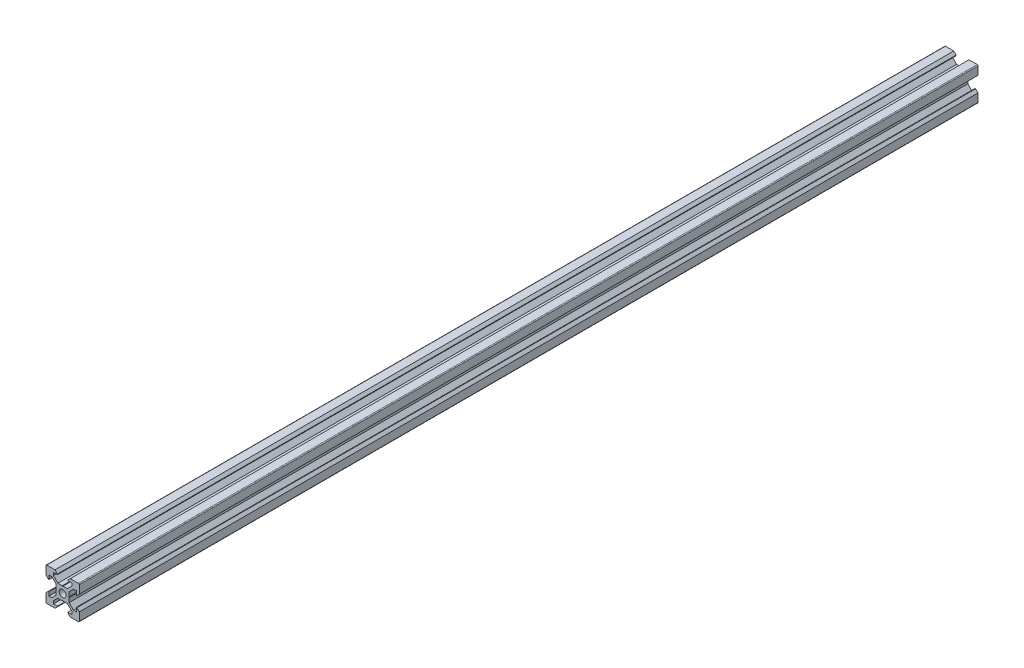
SolidWorks part; units mm, degrees
material "6061-T6 (SS)"
ref_plane "Front Plane" through (0, 0, 0) normal (0, 0, 1) x (1, 0, 0)
ref_plane "Top Plane" through (0, 0, 0) normal (0, 1, 0) x (1, 0, 0)
ref_plane "Right Plane" through (0, 0, 0) normal (1, 0, 0) x (0, 0, -1)
sketch "Sketch1" plane through (0, 0, 0) normal (0, 0, 1) x (1, 0, 0)
  line L1 (9.5, -10) -> (-9.5, -10)
  line L2 (10, -9.5) -> (10, 9.5)
  line L3 (9.5, 10) -> (-9.5, 10)
  line L4 (-10, -9.5) -> (-10, 9.5)
  line L5 (10, -10) -> (-10, 10) construction
  line L6 (10, 10) -> (-10, -10) construction
  circle A0 centre (0, 0) radius 2.1
  arc A1 (-9.5, 10) -> (-10, 9.5) centre (-9.5, 9.5) ccw
  arc A2 (10, 9.5) -> (9.5, 10) centre (9.5, 9.5) ccw
  arc A3 (9.5, -10) -> (10, -9.5) centre (9.5, -9.5) ccw
  arc A4 (-9.5, -10) -> (-10, -9.5) centre (-9.5, -9.5) cw
  point P0 (0, 0)
  line B0 (0, 0) -> (0, 10) construction
  line B1 (0, 3.69) -> (-0.21, 3.9)
  line B2 (-0.21, 3.9) -> (-2.8393, 3.9)
  line B3 (-2.8393, 3.9) -> (-5.5, 6.5607)
  line B4 (-5.5, 6.5607) -> (-5.5, 8.2)
  line B5 (-5.5, 8.2) -> (-3.125, 8.2)
  line B6 (-3.125, 8.2) -> (-3.125, 8.545)
  line B7 (-3.125, 8.545) -> (-4.58, 10)
  line B8 (-4.58, 10) -> (4.58, 10)
  line B9 (0, 0) -> (-5.9132, 5.9132) construction
  line B10 (3.125, 8.545) -> (4.58, 10)
  line B11 (3.125, 8.2) -> (3.125, 8.545)
  line B12 (5.5, 8.2) -> (3.125, 8.2)
  line B13 (5.5, 6.5607) -> (5.5, 8.2)
  line B14 (2.8393, 3.9) -> (5.5, 6.5607)
  line B15 (0.21, 3.9) -> (2.8393, 3.9)
  line B16 (0, 3.69) -> (0.21, 3.9)
  line B17 (0, 0) -> (-10, 0) construction
  line B18 (-3.69, 0) -> (-3.9, -0.21)
  line B19 (-3.9, -0.21) -> (-3.9, -2.8393)
  line B20 (-3.9, -2.8393) -> (-6.5607, -5.5)
  line B21 (-6.5607, -5.5) -> (-8.2, -5.5)
  line B22 (-8.2, -5.5) -> (-8.2, -3.125)
  line B23 (-8.2, -3.125) -> (-8.545, -3.125)
  line B24 (-8.545, -3.125) -> (-10, -4.58)
  line B25 (-10, -4.58) -> (-10, 4.58)
  line B26 (0, 0) -> (-5.9132, -5.9132) construction
  line B27 (-8.545, 3.125) -> (-10, 4.58)
  line B28 (-8.2, 3.125) -> (-8.545, 3.125)
  line B29 (-8.2, 5.5) -> (-8.2, 3.125)
  line B30 (-6.5607, 5.5) -> (-8.2, 5.5)
  line B31 (-3.9, 2.8393) -> (-6.5607, 5.5)
  line B32 (-3.9, 0.21) -> (-3.9, 2.8393)
  line B33 (-3.69, 0) -> (-3.9, 0.21)
  line B34 (0, 0) -> (0, -10) construction
  line B35 (0, -3.69) -> (0.21, -3.9)
  line B36 (0.21, -3.9) -> (2.8393, -3.9)
  line B37 (2.8393, -3.9) -> (5.5, -6.5607)
  line B38 (5.5, -6.5607) -> (5.5, -8.2)
  line B39 (5.5, -8.2) -> (3.125, -8.2)
  line B40 (3.125, -8.2) -> (3.125, -8.545)
  line B41 (3.125, -8.545) -> (4.58, -10)
  line B42 (4.58, -10) -> (-4.58, -10)
  line B43 (0, 0) -> (5.9132, -5.9132) construction
  line B44 (-3.125, -8.545) -> (-4.58, -10)
  line B45 (-3.125, -8.2) -> (-3.125, -8.545)
  line B46 (-5.5, -8.2) -> (-3.125, -8.2)
  line B47 (-5.5, -6.5607) -> (-5.5, -8.2)
  line B48 (-2.8393, -3.9) -> (-5.5, -6.5607)
  line B49 (-0.21, -3.9) -> (-2.8393, -3.9)
  line B50 (0, -3.69) -> (-0.21, -3.9)
  line B51 (0, 0) -> (10, 0) construction
  line B52 (3.69, 0) -> (3.9, 0.21)
  line B53 (3.9, 0.21) -> (3.9, 2.8393)
  line B54 (3.9, 2.8393) -> (6.5607, 5.5)
  line B55 (6.5607, 5.5) -> (8.2, 5.5)
  line B56 (8.2, 5.5) -> (8.2, 3.125)
  line B57 (8.2, 3.125) -> (8.545, 3.125)
  line B58 (8.545, 3.125) -> (10, 4.58)
  line B59 (10, 4.58) -> (10, -4.58)
  line B60 (0, 0) -> (5.9132, 5.9132) construction
  line B61 (8.545, -3.125) -> (10, -4.58)
  line B62 (8.2, -3.125) -> (8.545, -3.125)
  line B63 (8.2, -5.5) -> (8.2, -3.125)
  line B64 (6.5607, -5.5) -> (8.2, -5.5)
  line B65 (3.9, -2.8393) -> (6.5607, -5.5)
  line B66 (3.9, -0.21) -> (3.9, -2.8393)
  line B67 (3.69, 0) -> (3.9, -0.21)
  dimension "D1" = 4.2
  dimension "D3" = 0.5
  dimension "D2" = 20
sketch_block_instance "V Slot 1-4"
sketch_block "V Slot 1" parameters "D1"=10, "D2"=11, "D3"=4.3, "D4"=1.8, "D5"=0.21, "D6"=45, "D7"=9.16, "D8"=1.5, "D9"=6.25
sketch_block_instance "V Slot 1-5"
sketch_block_instance "V Slot 1-6"
sketch_block_instance "V Slot 1-7"
extrude "Boss-Extrude1" add sketch "Sketch1" along normal blind 540 contours B67 B52 B53 B54 B55 B56 B57 B58 L2 A2 L3 B10 B11 B12 B13 B14 B15 B16 B1 B2 B3 B4 B5 B6 B7 A1 L4 B27 B28 B29 B30 B31 B32 B33 B18 B19 B20 B21 B22 B23 B24 A4 L1 B44 B45 B46 B47 B48 B49
